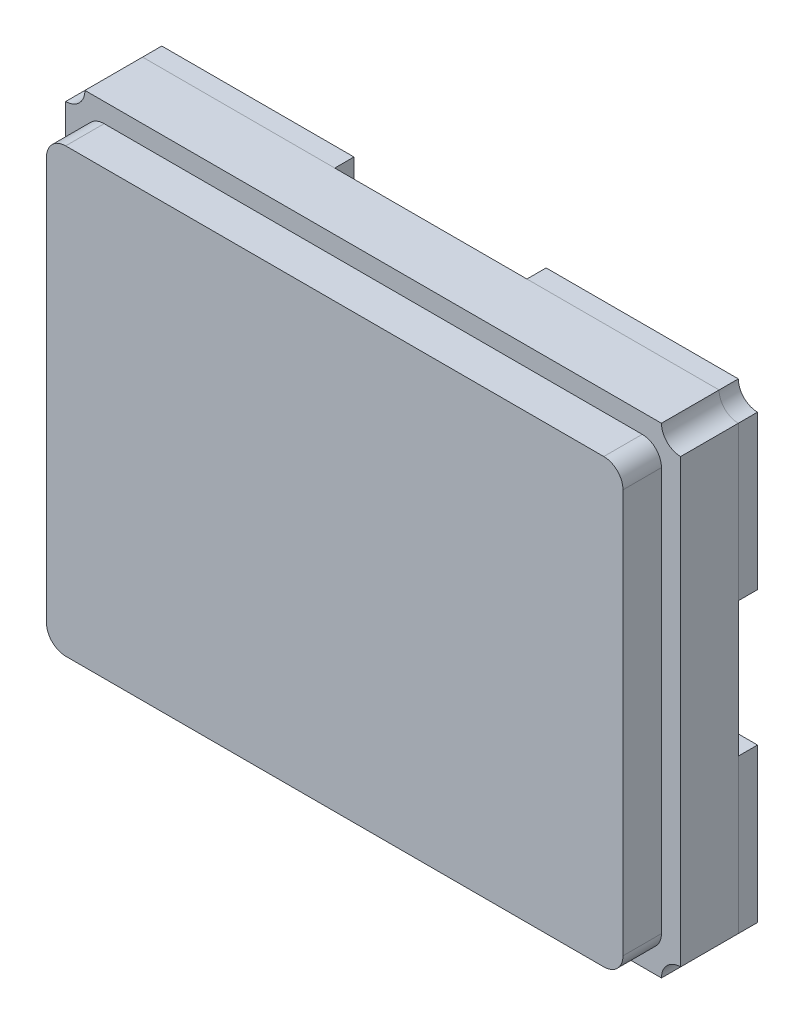
SolidWorks part; units mm, degrees
ref_plane "Front Plane" through (0, 0, 0) normal (0, 0, 1) x (1, 0, 0)
ref_plane "Top Plane" through (0, 0, 0) normal (0, 1, 0) x (1, 0, 0)
ref_plane "Right Plane" through (0, 0, 0) normal (1, 0, 0) x (0, 0, -1)
sketch "Sketch1" plane through (0, 0, 0) normal (0, 0, 1) x (1, 0, 0)
  line L0 (0, 2.4) -> (0, 2.5) construction
  line L1 (0.1, 0) -> (3.1, 0)
  line L2 (0, 0.1) -> (0, 2.4)
  line L3 (0.1, 2.5) -> (3.1, 2.5)
  line L4 (3.2, 0.1) -> (3.2, 2.4)
  line L5 (0, 2.5) -> (0.1, 2.5) construction
  line L6 (3.1, 2.5) -> (3.2, 2.5) construction
  line L7 (3.2, 2.5) -> (3.2, 2.4) construction
  line L8 (3.2, 0.1) -> (3.2, 0) construction
  line L9 (3.2, 0) -> (3.1, 0) construction
  line L10 (0.1, 0) -> (0, 0) construction
  line L11 (0, 0) -> (0, 0.1) construction
  arc A0 (0.1, 2.5) -> (0, 2.4) centre (0, 2.5) cw
  arc A1 (0, 0.1) -> (0.1, 0) centre (0, 0) cw
  arc A2 (3.1, 0) -> (3.2, 0.1) centre (3.2, 0) cw
  arc A3 (3.1, 2.5) -> (3.2, 2.4) centre (3.2, 2.5) ccw
  dimension "D3" = 0.1
  dimension "D1" = 3.2
  dimension "D2" = 2.5
extrude "Boss-Extrude1" add sketch "Sketch1" along normal blind 0.3
sketch "Sketch2" plane through (0, 0, 0.3) normal (0, 0, 1) x (1, 0, 0)
  line L0 (0, 1.25) -> (3.2, 1.25) construction
  line L1 (0, 2.4) -> (0, 0.1) construction
  line L2 (3.2, 0.1) -> (3.2, 2.4) construction
  line L4 (3.1, 2.5) -> (0.1, 2.5) construction
  line L5 (1.6, 2.5) -> (1.6, 0) construction
  line L6 (0.1, 0) -> (3.1, 0) construction
  line L7 (0.1, 2.4) -> (3.1, 2.4)
  line L8 (0.1, 2.4) -> (0.1, 0.1)
  line L9 (0.1, 0.1) -> (3.1, 0.1)
  line L10 (3.1, 2.4) -> (3.1, 0.1)
  point P16 (1.6, 2.4)
  point P17 (0.1, 1.25)
  dimension "D1" = 2.3
  dimension "D2" = 3
extrude "Boss-Extrude2" add sketch "Sketch2" along normal blind 0.2
fillet "Fillet1" radius 0.1 4 edges at (0.1, 0.1, 0.4) (0.1, 2.4, 0.4) (3.1, 2.4, 0.4) (3.1, 0.1, 0.4)
sketch "Sketch3" plane through (0, 0, 0) normal (0, 0, -1) x (-1, 0, 0)
  line L0 (-3.1, 2.5) -> (-0.1, 2.5) construction
  line L1 (-2.1, 2.5) -> (-3.1, 2.5)
  line L2 (-2.1, 2.5) -> (-2.1, 1.6)
  line L3 (-2.1, 1.6) -> (-3.2, 1.6)
  line L4 (-3.2, 2.4) -> (-3.2, 1.6)
  line L5 (-3.2, 0.1) -> (-3.2, 2.4) construction
  line L6 (0, 2.4) -> (0, 0.1) construction
  line L7 (-1.1, 2.5) -> (-0.1, 2.5)
  line L8 (-1.1, 2.5) -> (-1.1, 1.6)
  line L9 (-1.1, 1.6) -> (0, 1.6)
  line L10 (0, 2.4) -> (0, 1.6)
  line L11 (-1.6, 2.5) -> (-1.6, 0) construction
  line L12 (-1.1, 0.9) -> (0, 0.9)
  line L13 (-1.1, 0.9) -> (-1.1, 0)
  line L14 (-1.1, 0) -> (-0.1, 0)
  line L15 (0, 0.9) -> (0, 0.1)
  line L16 (-2.1, 0.9) -> (-3.2, 0.9)
  line L17 (-2.1, 0.9) -> (-2.1, 0)
  line L18 (-2.1, 0) -> (-3.1, 0)
  line L19 (-3.2, 0.9) -> (-3.2, 0.1)
  line L20 (-0.1, 0) -> (-3.1, 0) construction
  line L22 (-3.2, 1.25) -> (0, 1.25) construction
  arc A0 (-0.1, 2.5) -> (0, 2.4) centre (0, 2.5) ccw
  arc A1 (-0.1, 2.5) -> (0, 2.4) centre (0, 2.5) ccw construction
  arc A2 (-0.1, 0) -> (0, 0.1) centre (0, 0) cw
  arc A3 (-3.2, 0.1) -> (-3.1, 0) centre (-3.2, 0) cw
  arc A4 (-3.1, 2.5) -> (-3.2, 2.4) centre (-3.2, 2.5) cw
  dimension "D3" = 0.1
  dimension "D1" = 0.7
  dimension "D2" = 1
  dimension "D4" = 0.9
  dimension "D5" = 0.9
extrude "Boss-Extrude3" add sketch "Sketch3" along normal blind 0.1 separate body
